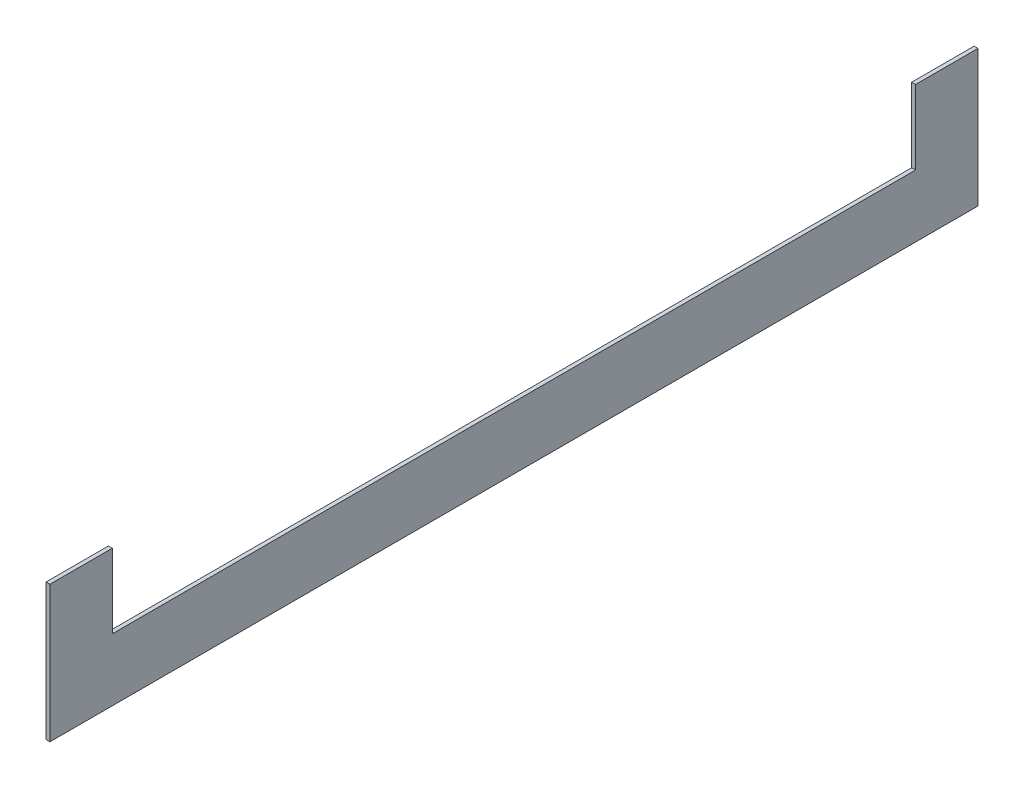
SolidWorks part; units mm, degrees
ref_plane "Front Plane" through (0, 0, 0) normal (0, 0, 1) x (1, 0, 0)
ref_plane "Top Plane" through (0, 0, 0) normal (0, 1, 0) x (1, 0, 0)
ref_plane "Right Plane" through (0, 0, 0) normal (1, 0, 0) x (0, 0, -1)
sketch "Sketch1" plane through (0, 0, 0) normal (1, 0, 0) x (0, 0, -1)
  line L0 (-377.825, 0) -> (377.825, 0)
  line L1 (-377.825, 0) -> (-377.825, 111.125)
  line L2 (-377.825, 111.125) -> (-327.025, 111.125)
  line L3 (-327.025, 111.125) -> (-327.025, 50.8)
  line L4 (-327.025, 50.8) -> (327.025, 50.8)
  line L5 (327.025, 50.8) -> (327.025, 111.125)
  line L6 (327.025, 111.125) -> (377.825, 111.125)
  line L7 (377.825, 111.125) -> (377.825, 0)
  point P2 (0, 0)
  dimension "D1" = 755.65
  dimension "D2" = 50.8
  dimension "D3" = 50.8
  dimension "D4" = 60.325
extrude "Boss-Extrude1" add sketch "Sketch1" along normal blind 3.175
